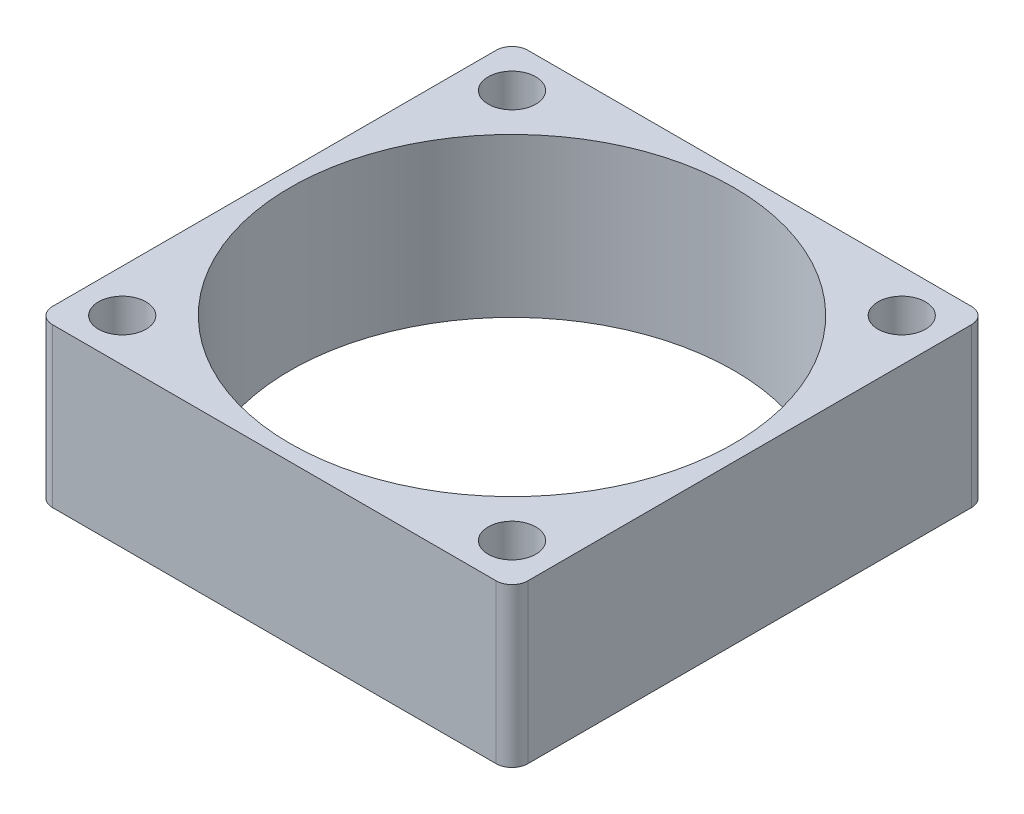
SolidWorks part; units mm, degrees
ref_plane "前视基准面" through (0, 0, 0) normal (0, 0, 1) x (1, 0, 0)
ref_plane "上视基准面" through (0, 0, 0) normal (0, 1, 0) x (1, 0, 0)
ref_plane "右视基准面" through (0, 0, 0) normal (1, 0, 0) x (0, 0, -1)
sketch "草图1" plane through (0, 0, 0) normal (0, 1, 0) x (1, 0, 0)
  line L1 (-15, 15) -> (15, 15)
  line L2 (-15, 15) -> (-15, -15)
  line L3 (-15, -15) -> (15, -15)
  line L4 (15, 15) -> (15, -15)
  line L5 (-15, 15) -> (15, -15) construction
  line L6 (-15, -15) -> (15, 15) construction
  point P0 (0, 0)
  dimension "D1" = 30
  dimension "D2" = 30
extrude "凸台-拉伸1" add sketch "草图1" along normal blind 10
sketch "草图2" plane through (0, 10, 0) normal (0, 1, 0) x (1, 0, 0)
  line L0 (15, 15) -> (-15, 15) construction
  line L1 (-15, 15) -> (-15, -15) construction
  line L2 (15, -15) -> (15, 15) construction
  line L3 (-15, -15) -> (15, -15) construction
  circle A0 centre (-12.3, 12.3) radius 1.5
  circle A1 centre (12.3, 12.3) radius 1.5
  circle A2 centre (-12.3, -12.3) radius 1.5
  circle A3 centre (12.3, -12.3) radius 1.5
  dimension "D1" = 3
  dimension "D2" = 2.7
  dimension "D3" = 2.7
  dimension "D4" = 2.7
  dimension "D5" = 2.7
extrude "切除-拉伸1" cut sketch "草图2" against normal through all
fillet "圆角1" radius 1 4 edges at (-15, 5, -15) (-15, 5, 15) (15, 5, 15) (15, 5, -15)
sketch "草图3" plane through (0, 10, 0) normal (0, 1, 0) x (1, 0, 0)
  circle A0 centre (0, 0) radius 14
  dimension "D1" = 28
extrude "切除-拉伸2" cut sketch "草图3" against normal through all
